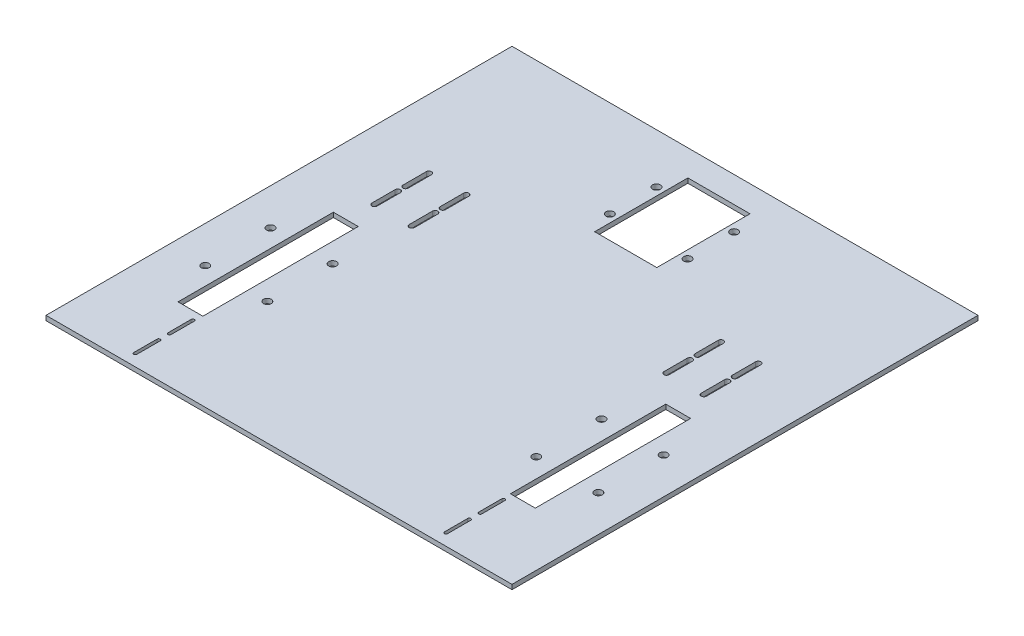
SolidWorks part; units mm, degrees
ref_plane "Front Plane" through (0, 0, 0) normal (0, 0, 1) x (1, 0, 0)
ref_plane "Top Plane" through (0, 0, 0) normal (0, 1, 0) x (1, 0, 0)
ref_plane "Right Plane" through (0, 0, 0) normal (1, 0, 0) x (0, 0, -1)
sketch "Sketch1" plane through (0, 0, 0) normal (0, 1, 0) x (1, 0, 0)
  line L0 (0, 0) -> (0, 150) construction
  line L5 (-150, -150) -> (150, -150)
  line L6 (-150, -150) -> (-150, 150)
  line L7 (-150, 150) -> (150, 150)
  line L8 (150, -150) -> (150, 150)
  line L9 (-150, -150) -> (150, 150) construction
  line L10 (-150, 150) -> (150, -150) construction
  line L11 (0, 0) -> (0, -150) construction
  point P0 (0, 0)
  dimension "D1" = 300
  dimension "D2" = 300
extrude "Boss-Extrude1" add sketch "Sketch1" along normal blind 3
sketch "Sketch2" plane through (0, 3, 0) normal (0, 1, 0) x (1, 0, 0)
  line L0 (-107, -49.9975) -> (-150, -49.9975) construction
  line L1 (-115, 0.0025) -> (-99, 0.0025)
  line L2 (-115, 0.0025) -> (-115, -99.9975)
  line L3 (-115, -99.9975) -> (-99, -99.9975)
  line L4 (-99, 0.0025) -> (-99, -99.9975)
  line L5 (-115, 0.0025) -> (-99, -99.9975) construction
  line L6 (-115, -99.9975) -> (-99, 0.0025) construction
  line L7 (-150, 150) -> (-150, -150) construction
  point P0 (-107, -49.9975)
  dimension "D1" = 43
sketch "Sketch3" plane through (0, 3, 0) normal (0, 1, 0) x (1, 0, 0)
  line L0 (106.9979, -50.0021) -> (150, -50.0021) construction
  line L1 (98.9979, -0.0021) -> (114.9979, -0.0021)
  line L2 (98.9979, -0.0021) -> (98.9979, -100.0021)
  line L3 (98.9979, -100.0021) -> (114.9979, -100.0021)
  line L4 (114.9979, -0.0021) -> (114.9979, -100.0021)
  line L5 (98.9979, -0.0021) -> (114.9979, -100.0021) construction
  line L6 (98.9979, -100.0021) -> (114.9979, -0.0021) construction
  line L7 (150, -150) -> (150, 150) construction
  point P0 (106.9979, -50.0021)
  dimension "D1" = 43.0021
sketch "Sketch4" plane through (0, 3, 0) normal (0, 1, 0) x (1, 0, 0)
  line L0 (-150, -49.99) -> (-115, -49.99) construction
  line L1 (-150, 150) -> (-150, -150) construction
  line L2 (-115, 0.0025) -> (-115, -99.9975) construction
  line L3 (114.9979, -50.0021) -> (150, -50.0021) construction
  line L4 (114.9979, -0.0021) -> (114.9979, -100.0021) construction
  line L5 (150, -150) -> (150, 150) construction
  line L6 (106.9979, -100.0021) -> (106.9979, -150) construction
  line L7 (98.9979, -100.0021) -> (114.9979, -100.0021) construction
  line L8 (-150, -150) -> (150, -150) construction
  line L9 (-107, -99.9975) -> (-107, -150) construction
  line L10 (-115, -99.9975) -> (-99, -99.9975) construction
  dimension "D1" = 35
  dimension "D2" = 35.0021
  dimension "D3" = 49.9979
  dimension "D4" = 50.0025
extrude "Cut-Extrude2" cut sketch "Sketch2" against normal blind 3
extrude "Cut-Extrude3" cut sketch "Sketch3" against normal blind 3
sketch "Sketch5" plane through (0, 3, 0) normal (0, 1, 0) x (1, 0, 0)
  line L1 (-19.9998, 133.2218) -> (20.0002, 133.2218)
  line L2 (-19.9998, 133.2218) -> (-19.9998, 73.2218)
  line L3 (-19.9998, 73.2218) -> (20.0002, 73.2218)
  line L4 (20.0002, 133.2218) -> (20.0002, 73.2218)
  line L5 (-19.9998, 133.2218) -> (20.0002, 73.2218) construction
  line L6 (-19.9998, 73.2218) -> (20.0002, 133.2218) construction
  point P0 (0.0002, 103.2218)
extrude "Cut-Extrude4" cut sketch "Sketch5" against normal blind 3
sketch "Sketch6" plane through (0, 3, 0) normal (0, 1, 0) x (1, 0, 0)
  line L0 (-126.4658, -29.0191) -> (-126.4658, -71.0191) construction
  line L1 (126.6814, -29.0751) -> (126.6814, -71.0751) construction
  line L2 (-86.4658, -29.0191) -> (-86.4658, -71.0191) construction
  line L3 (86.6814, -29.0751) -> (86.6814, -71.0751) construction
  line L4 (-25, 118) -> (-25, 88) construction
  line L5 (-25, 88) -> (25, 88) construction
  line L6 (-126.4658, -29.0191) -> (-86.4658, -29.0191) construction
  line L8 (86.6814, -29.0751) -> (126.6814, -29.0751) construction
  line L9 (-126.4658, -29.0191) -> (-86.4658, -71.0191) construction
  line L10 (-86.4658, -29.0191) -> (-126.4658, -71.0191) construction
  line L11 (-115, -49.99) -> (-106.4658, -50.0191) construction
  line L12 (86.6814, -29.0751) -> (126.6814, -71.0751) construction
  line L13 (126.6814, -29.0751) -> (86.6814, -71.0751) construction
  line L14 (114.9979, -50.0021) -> (106.6814, -50.0751) construction
  line L15 (-25, 118) -> (25, 118) construction
  line L16 (25, 118) -> (25, 88) construction
  circle A0 centre (-126.4658, -29.0191) radius 2.5
  circle A1 centre (-86.4658, -29.0191) radius 2.5
  circle A2 centre (-126.4658, -71.0191) radius 2.5
  circle A3 centre (-86.4658, -71.0191) radius 2.5
  circle A4 centre (86.6814, -29.0751) radius 2.5
  circle A5 centre (86.6814, -71.0751) radius 2.5
  circle A6 centre (126.6814, -29.0751) radius 2.5
  circle A7 centre (126.6814, -71.0751) radius 2.5
  circle A8 centre (-25, 118) radius 2.5
  circle A9 centre (-25, 88) radius 2.5
  circle A10 centre (25, 118) radius 2.5
  circle A11 centre (25, 88) radius 2.5
  dimension "D1" = 42
  dimension "D2" = 42
  dimension "D3" = 42
  dimension "D4" = 42
  dimension "D5" = 50
  dimension "D6" = 30
  dimension "D7" = 40
  dimension "D8" = 40
extrude "Cut-Extrude5" cut sketch "Sketch6" against normal blind 3
sketch "Sketch7" plane through (0, 3, 0) normal (0, 1, 0) x (1, 0, 0)
  line L0 (-106, 52.5) -> (-106, 37.5) construction
  line L1 (-104.3, 52.5) -> (-104.3, 37.5)
  line L2 (-107.7, 52.5) -> (-107.7, 37.5)
  line L3 (-106, 32.5) -> (-106, 17.5) construction
  line L4 (-104.3, 32.5) -> (-104.3, 17.5)
  line L5 (-107.7, 32.5) -> (-107.7, 17.5)
  line L6 (-82, 52.5) -> (-82, 37.5) construction
  line L7 (-80.3, 52.5) -> (-80.3, 37.5)
  line L8 (-83.7, 52.5) -> (-83.7, 37.5)
  line L9 (-82, 32.5) -> (-82, 17.5) construction
  line L10 (-80.3, 32.5) -> (-80.3, 17.5)
  line L11 (-83.7, 32.5) -> (-83.7, 17.5)
  line L14 (82, 52.5) -> (82, 37.5) construction
  line L15 (83.7, 52.5) -> (83.7, 37.5)
  line L16 (80.3, 52.5) -> (80.3, 37.5)
  line L17 (82, 32.5) -> (82, 17.5) construction
  line L18 (83.7, 32.5) -> (83.7, 17.5)
  line L19 (80.3, 32.5) -> (80.3, 17.5)
  line L20 (106, 52.5) -> (106, 37.5) construction
  line L21 (107.7, 52.5) -> (107.7, 37.5)
  line L22 (104.3, 52.5) -> (104.3, 37.5)
  line L23 (106, 32.5) -> (106, 17.5) construction
  line L24 (107.7, 32.5) -> (107.7, 17.5)
  line L25 (104.3, 32.5) -> (104.3, 17.5)
  arc A0 (-104.3, 52.5) -> (-107.7, 52.5) centre (-106, 52.5) ccw
  arc A1 (-107.7, 37.5) -> (-104.3, 37.5) centre (-106, 37.5) ccw
  arc A2 (-104.3, 32.5) -> (-107.7, 32.5) centre (-106, 32.5) ccw
  arc A3 (-107.7, 17.5) -> (-104.3, 17.5) centre (-106, 17.5) ccw
  arc A4 (-80.3, 52.5) -> (-83.7, 52.5) centre (-82, 52.5) ccw
  arc A5 (-83.7, 37.5) -> (-80.3, 37.5) centre (-82, 37.5) ccw
  arc A6 (-80.3, 32.5) -> (-83.7, 32.5) centre (-82, 32.5) ccw
  arc A7 (-83.7, 17.5) -> (-80.3, 17.5) centre (-82, 17.5) ccw
  arc A8 (83.7, 52.5) -> (80.3, 52.5) centre (82, 52.5) ccw
  arc A9 (80.3, 37.5) -> (83.7, 37.5) centre (82, 37.5) ccw
  arc A10 (83.7, 32.5) -> (80.3, 32.5) centre (82, 32.5) ccw
  arc A11 (80.3, 17.5) -> (83.7, 17.5) centre (82, 17.5) ccw
  arc A12 (107.7, 52.5) -> (104.3, 52.5) centre (106, 52.5) ccw
  arc A13 (104.3, 37.5) -> (107.7, 37.5) centre (106, 37.5) ccw
  arc A14 (107.7, 32.5) -> (104.3, 32.5) centre (106, 32.5) ccw
  arc A15 (104.3, 17.5) -> (107.7, 17.5) centre (106, 17.5) ccw
  point P2 (-106, 45)
  point P9 (-106, 25)
  point P16 (-82, 45)
  point P23 (-82, 25)
  point P34 (82, 45)
  point P41 (82, 25)
  point P48 (106, 45)
  point P55 (106, 25)
extrude "Cut-Extrude6" cut sketch "Sketch7" against normal blind 3
sketch "Sketch8" plane through (0, 3, 0) normal (0, 1, 0) x (1, 0, 0)
  line L0 (-100, -105.5) -> (-100, -120.5) construction
  line L1 (-99, -105.5) -> (-99, -120.5)
  line L2 (-101, -105.5) -> (-101, -120.5)
  line L3 (-100, -127.5) -> (-100, -142.5) construction
  line L4 (-99, -127.5) -> (-99, -142.5)
  line L5 (-101, -127.5) -> (-101, -142.5)
  line L18 (100, -105.5) -> (100, -120.5) construction
  line L19 (101, -105.5) -> (101, -120.5)
  line L20 (99, -105.5) -> (99, -120.5)
  line L21 (100, -127.5) -> (100, -142.5) construction
  line L22 (101, -127.5) -> (101, -142.5)
  line L23 (99, -127.5) -> (99, -142.5)
  arc A0 (-99, -105.5) -> (-101, -105.5) centre (-100, -105.5) ccw
  arc A1 (-101, -120.5) -> (-99, -120.5) centre (-100, -120.5) ccw
  arc A2 (-99, -127.5) -> (-101, -127.5) centre (-100, -127.5) ccw
  arc A3 (-101, -142.5) -> (-99, -142.5) centre (-100, -142.5) ccw
  arc A12 (101, -105.5) -> (99, -105.5) centre (100, -105.5) ccw
  arc A13 (99, -120.5) -> (101, -120.5) centre (100, -120.5) ccw
  arc A14 (101, -127.5) -> (99, -127.5) centre (100, -127.5) ccw
  arc A15 (99, -142.5) -> (101, -142.5) centre (100, -142.5) ccw
  point P2 (-100, -113)
  point P9 (-100, -135)
  point P46 (100, -113)
  point P53 (100, -135)
extrude "Cut-Extrude7" cut sketch "Sketch8" against normal blind 3
